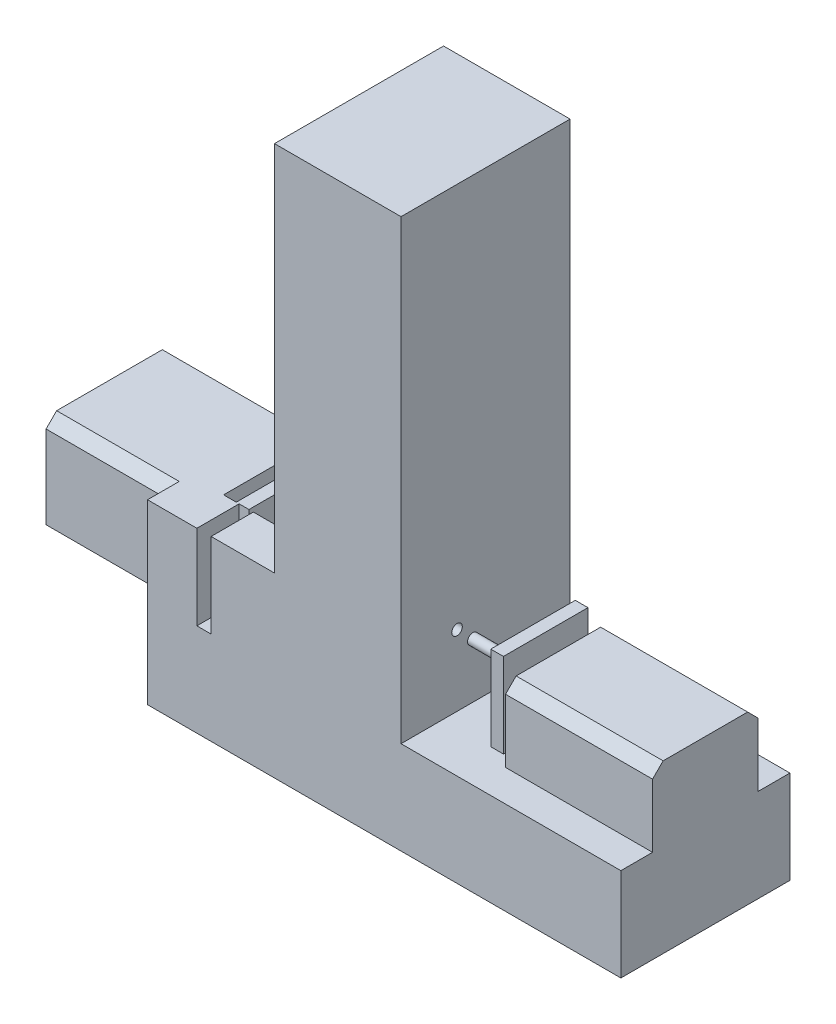
SolidWorks part; units mm, degrees
ref_plane "Front Plane" through (0, 0, 0) normal (0, 0, 1) x (1, 0, 0)
ref_plane "Top Plane" through (0, 0, 0) normal (0, 1, 0) x (1, 0, 0)
ref_plane "Right Plane" through (0, 0, 0) normal (1, 0, 0) x (0, 0, -1)
sketch "Sketch1" plane through (0, 0, 0) normal (0, 1, 0) x (1, 0, 0)
  line L1 (0, 0) -> (284.48, 0)
  line L2 (0, 0) -> (0, 101.6)
  line L3 (0, 101.6) -> (284.48, 101.6)
  line L4 (284.48, 0) -> (284.48, 101.6)
  dimension "D1" = 284.48
  dimension "D2" = 101.6
extrude "Boss-Extrude1" add sketch "Sketch1" along normal blind 55.88
sketch "Sketch2" plane through (0, 55.88, 0) normal (0, 1, 0) x (1, 0, 0)
  line L0 (284.48, 101.6) -> (0, 101.6) construction
  line L1 (76.3161, 101.6) -> (152.3585, 101.6)
  line L2 (76.3161, 101.6) -> (76.3161, 0)
  line L3 (76.3161, 0) -> (152.3585, 0)
  line L4 (152.3585, 101.6) -> (152.3585, 0)
  line L5 (0, 0) -> (284.48, 0) construction
extrude "Boss-Extrude2" add sketch "Sketch2" along normal blind 274.32
ref_plane "Plane1" through (0, 203.2, 0) normal (0, 1, 0) x (1, 0, 0)
sketch "Sketch3" plane through (0, 203.2, 0) normal (0, 1, 0) x (1, 0, 0)
  line L0 (76.3161, 101.6) -> (76.3161, 0) construction
  line L5 (58.8357, 36.83) -> (127.1161, 36.83)
  line L10 (58.8357, 36.83) -> (58.8357, 30.48)
  line L11 (58.8357, 30.48) -> (127.1161, 30.48)
  line L12 (58.8357, 71.12) -> (127.1161, 71.12)
  line L13 (58.8357, 71.12) -> (58.8357, 64.77)
  line L14 (58.8357, 64.77) -> (127.1161, 64.77)
  line L15 (127.1161, 71.12) -> (127.1161, 64.77)
  line L16 (127.1161, 36.83) -> (127.1161, 30.48)
  line L17 (152.3585, 101.6) -> (76.3161, 101.6) construction
  dimension "D1" = 50.8
  dimension "D2" = 50.8
  dimension "D3" = 6.35
  dimension "D4" = 6.35
  dimension "D5" = 27.94
  dimension "D6" = 30.48
extrude "Cut-Extrude1" cut sketch "Sketch3" against normal up to surface (147.32 mm away) up to face at (38.1581, 55.88, -50.8)
sketch "Sketch4" plane through (127.1161, 0, 0) normal (-1, 0, 0) x (0, 0, 1)
  line L1 (-30.48, 203.2) -> (-30.48, 55.88) construction
  line L2 (-64.77, 203.2) -> (-64.77, 55.88) construction
  line L3 (-64.77, 55.88) -> (-71.12, 55.88) construction
  circle A0 centre (-33.655, 98.425) radius 3.175
  circle A1 centre (-67.945, 64.135) radius 3.175
  point P2 (0, 0)
  point P6 (0, 0)
  point P9 (-73.1656, 62.23)
  point P12 (0, 0)
  dimension "D1" = 6.35
  dimension "D6" = 6.35
  dimension "D2" = 34.29
  dimension "D3" = 3.175
  dimension "D4" = 3.175
  dimension "D5" = 8.255
extrude "Cut-Extrude2" cut sketch "Sketch4" against normal blind 274.32
sketch "Sketch5" plane through (76.3161, 0, 0) normal (-1, 0, 0) x (0, 0, 1)
  line L0 (-101.6, 330.2) -> (-101.6, 55.88) construction
  line L1 (-101.6, 106.68) -> (-76.2, 106.68)
  line L2 (-101.6, 106.68) -> (-101.6, 55.88)
  line L3 (-101.6, 55.88) -> (-76.2, 55.88)
  line L4 (-76.2, 106.68) -> (-76.2, 55.88)
  line L5 (-101.6, 55.88) -> (0, 55.88) construction
  line L6 (0, 330.2) -> (0, 55.88) construction
  line L7 (0, 106.68) -> (-25.4, 106.68)
  line L8 (0, 106.68) -> (0, 55.88)
  line L9 (0, 55.88) -> (-25.4, 55.88)
  line L10 (-25.4, 106.68) -> (-25.4, 55.88)
  line L11 (-30.48, 55.88) -> (0, 55.88) construction
  dimension "D1" = 25.4
  dimension "D2" = 25.4
  dimension "D3" = 50.8
  dimension "D4" = 50.8
extrude "Boss-Extrude4" add sketch "Sketch5" along normal blind 38.1
sketch "Sketch6" plane through (0, 55.88, 0) normal (0, 1, 0) x (1, 0, 0)
  line L1 (0, 101.6) -> (29.6659, 101.6)
  line L2 (0, 101.6) -> (0, 76.2)
  line L3 (0, 76.2) -> (29.6659, 76.2)
  line L4 (29.6659, 101.6) -> (29.6659, 76.2)
  line L5 (29.6659, 25.4) -> (0, 25.4)
  line L6 (29.6659, 25.4) -> (29.6659, 0)
  line L7 (29.6659, 0) -> (0, 0)
  line L8 (0, 25.4) -> (0, 0)
extrude "Boss-Extrude5" add sketch "Sketch6" along normal up to surface (50.8 mm away) up to face at (57.2661, 106.68, -88.9)
ref_plane "Plane2" through (20.32, 0, 0) normal (-1, 0, 0) x (0, 0, 1)
sketch "Sketch7" plane through (20.32, 0, 0) normal (-1, 0, 0) x (0, 0, 1)
  line L0 (-76.2, 106.68) -> (-101.6, 106.68) construction
  line L1 (-88.9, 106.68) -> (-12.7, 106.68)
  line L2 (-88.9, 106.68) -> (-88.9, 44.1233)
  line L3 (-88.9, 44.1233) -> (-12.7, 44.1233)
  line L4 (-12.7, 106.68) -> (-12.7, 44.1233)
extrude "Boss-Extrude6" add sketch "Sketch7" along normal blind 93.98
sketch "Sketch8" plane through (20.32, 0, 0) normal (1, 0, 0) x (0, 0, -1)
  circle A0 centre (50.8, 81.28) radius 6.35
  dimension "D1" = 12.7
extrude "Boss-Extrude7" add sketch "Sketch8" along normal blind 7.62
sketch "Sketch9" plane through (27.94, 0, 0) normal (1, 0, 0) x (0, 0, -1)
  line L1 (25.4, 106.68) -> (76.2, 106.68)
  line L2 (25.4, 106.68) -> (25.4, 55.88)
  line L3 (25.4, 55.88) -> (76.2, 55.88)
  line L4 (76.2, 106.68) -> (76.2, 55.88)
extrude "Boss-Extrude8" add sketch "Sketch9" along normal blind 7.62
sketch "Sketch11" plane through (0, 55.88, 0) normal (0, 1, 0) x (1, 0, 0)
  line L0 (284.48, 0) -> (284.48, 101.6) construction
  line L1 (284.48, 82.55) -> (196.1238, 82.55)
  line L2 (284.48, 82.55) -> (284.48, 19.05)
  line L3 (284.48, 19.05) -> (196.1238, 19.05)
  line L4 (196.1238, 82.55) -> (196.1238, 19.05)
  line L5 (284.48, 101.6) -> (152.3585, 101.6) construction
  line L6 (152.3585, 0) -> (284.48, 0) construction
  dimension "D1" = 19.05
  dimension "D2" = 19.05
extrude "Boss-Extrude9" add sketch "Sketch11" along normal blind 44.45
sketch "Sketch13" plane through (196.1238, 0, 0) normal (-1, 0, 0) x (0, 0, 1)
  circle A0 centre (-50.8, 78.105) radius 6.35
  dimension "D1" = 12.7
extrude "Boss-Extrude10" add sketch "Sketch13" along normal blind 7.62
sketch "Sketch14" plane through (188.5038, 0, 0) normal (-1, 0, 0) x (0, 0, 1)
  line L1 (-76.2, 106.68) -> (-25.4, 106.68)
  line L2 (-76.2, 106.68) -> (-76.2, 55.88)
  line L3 (-76.2, 55.88) -> (-25.4, 55.88)
  line L4 (-25.4, 106.68) -> (-25.4, 55.88)
extrude "Boss-Extrude11" add sketch "Sketch14" along normal blind 7.62
sketch "Sketch15" plane through (180.8838, 0, 0) normal (-1, 0, 0) x (0, 0, 1)
  circle A0 centre (-33.655, 98.425) radius 3.175
  circle A1 centre (-67.945, 64.135) radius 3.175
extrude "Boss-Extrude12" add sketch "Sketch15" along normal blind 19.05
chamfer "Chamfer2" distance 6.35 6 edges at (240.3019, 100.33, -82.55) (240.3019, 100.33, -19.05) (-36.83, 44.1233, -88.9) (-36.83, 44.1233, -12.7) (-36.83, 106.68, -88.9) (-36.83, 106.68, -12.7)
